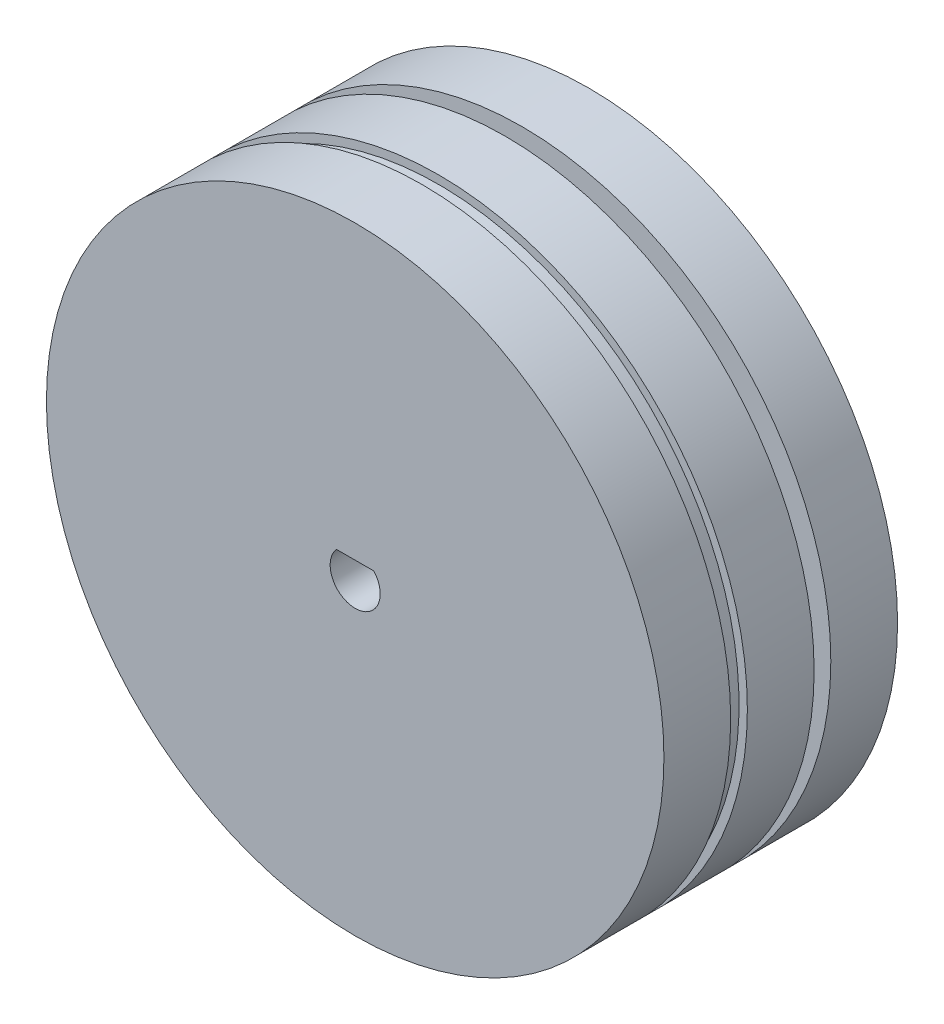
SolidWorks part; units mm, degrees
ref_plane "前视基准面" through (0, 0, 0) normal (0, 0, 1) x (1, 0, 0)
ref_plane "上视基准面" through (0, 0, 0) normal (0, 1, 0) x (1, 0, 0)
ref_plane "右视基准面" through (0, 0, 0) normal (1, 0, 0) x (0, 0, -1)
sketch "草图1" plane through (0, 0, 0) normal (0, 0, 1) x (1, 0, 0)
  circle A0 centre (0, 0) radius 18.5
  dimension "D1" = 37
extrude "凸台-拉伸1" add sketch "草图1" along normal blind 4
sketch "草图2" plane through (0, 0, 0) normal (0, 0, -1) x (-1, 0, 0)
  circle A0 centre (0, 0) radius 18
  dimension "D1" = 36
extrude "凸台-拉伸2" add sketch "草图2" along normal blind 1
sketch "草图3" plane through (0, 0, -1) normal (0, 0, -1) x (-1, 0, 0)
  circle A0 centre (0, 0) radius 18.5
  dimension "D1" = 37
extrude "凸台-拉伸3" add sketch "草图3" along normal blind 4
sketch "草图4" plane through (0, 0, -5) normal (0, 0, -1) x (-1, 0, 0)
  circle A0 centre (0, 0) radius 17
  dimension "D1" = 34
extrude "凸台-拉伸4" add sketch "草图4" along normal blind 1
sketch "草图5" plane through (0, 0, -6) normal (0, 0, -1) x (-1, 0, 0)
  circle A0 centre (0, 0) radius 18.5
  dimension "D1" = 37
extrude "凸台-拉伸5" add sketch "草图5" along normal blind 4
sketch "草图6" plane through (0, 0, 4) normal (0, 0, 1) x (1, 0, 0)
  line L0 (1.118, 1) -> (-1.118, 1)
  arc A0 (-1.118, 1) -> (1.118, 1) centre (0, 0) ccw
  dimension "D1" = 3
  dimension "D2" = 1
extrude "切除-拉伸1" cut sketch "草图6" against normal blind 6
sketch "草图7" plane through (0, 0, -10) normal (0, 0, -1) x (-1, 0, 0)
  circle A0 centre (0, 0) radius 3
  dimension "D1" = 6
extrude "切除-拉伸2" cut sketch "草图7" against normal blind 2.5
